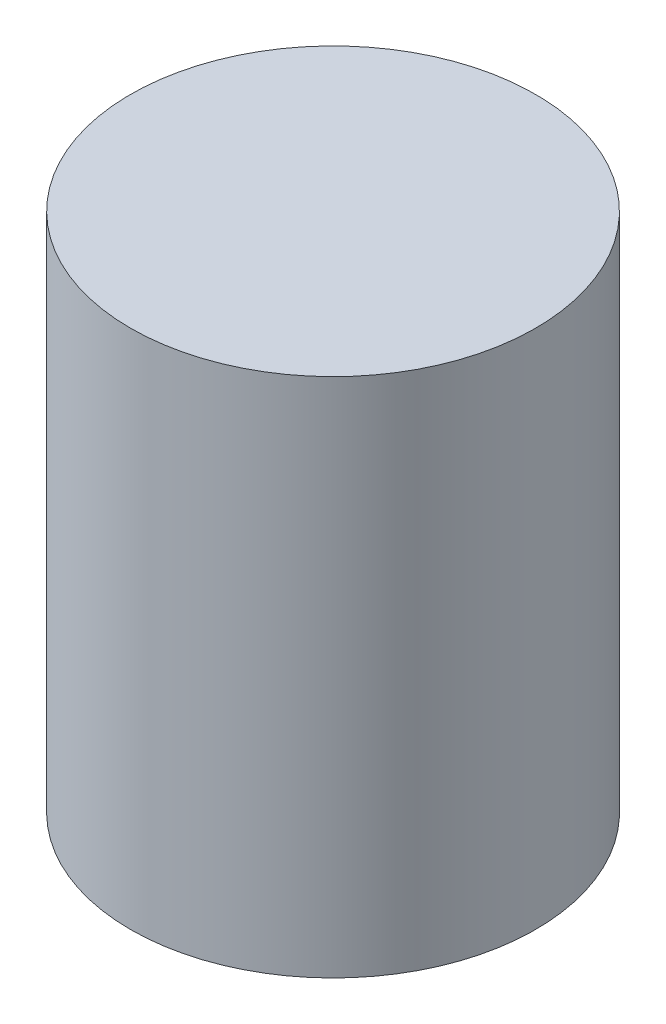
SolidWorks part; units mm, degrees
ref_plane "Front Plane" through (0, 0, 0) normal (0, 0, 1) x (1, 0, 0)
ref_plane "Top Plane" through (0, 0, 0) normal (0, 1, 0) x (1, 0, 0)
ref_plane "Right Plane" through (0, 0, 0) normal (1, 0, 0) x (0, 0, -1)
sketch "Sketch1" plane through (0, 0, 0) normal (0, 1, 0) x (1, 0, 0)
  circle A0 centre (0, 0) radius 17.5
  dimension "D1" = 35
extrude "Boss-Extrude1" add sketch "Sketch1" along normal blind 45
